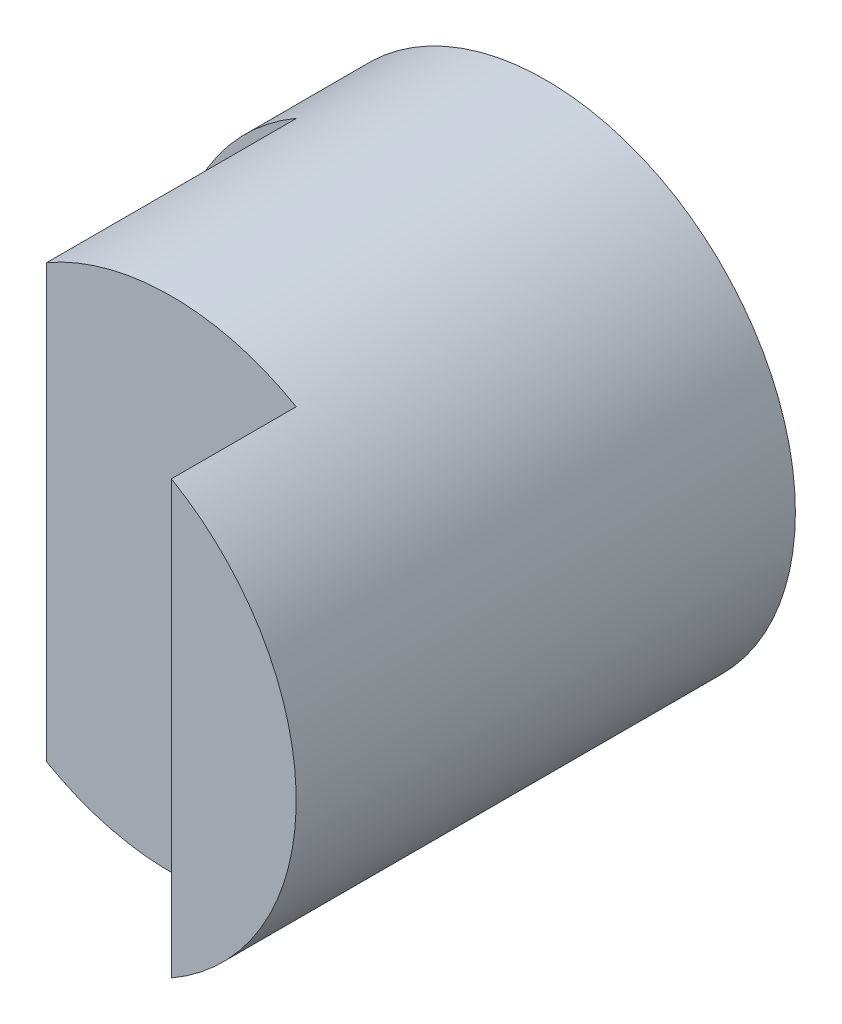
SolidWorks part; units mm, degrees
ref_plane "Front" through (0, 0, 0) normal (0, 0, 1) x (1, 0, 0)
ref_plane "Top" through (0, 0, 0) normal (0, 1, 0) x (1, 0, 0)
ref_plane "Right" through (0, 0, 0) normal (1, 0, 0) x (0, 0, -1)
sketch "Sketch1" plane through (0, 0, 0) normal (0, 0, 1) x (1, 0, 0)
  circle A0 centre (0, 0) radius 2
  dimension "D1" = 4
extrude "Boss-Extrude1" add sketch "Sketch1" along normal blind 4
sketch "Sketch2" plane through (0, 0, 0) normal (0, 1, 0) x (1, 0, 0)
  line L0 (-2, -4) -> (2, -4) construction
  line L1 (-1, -5) -> (1, -5)
  line L3 (-1, -3) -> (1, -3)
  line L4 (1, -5) -> (1, -3)
  line L5 (-1, -5) -> (1, -3) construction
  line L6 (-1, -3) -> (1, -5) construction
  line L7 (-1, -3) -> (-1, -0.9964)
  line L8 (-1, -0.9964) -> (-2, -0.9964)
  line L9 (-2, 0) -> (-2, -4) construction
  line L10 (-2, -0.9964) -> (-2, -5)
  line L11 (-2, -5) -> (-1, -5)
  point P0 (0, -4)
  dimension "D1" = 2
  dimension "D2" = 2
extrude "Cut-Extrude2" cut sketch "Sketch2" against normal mid plane 4
